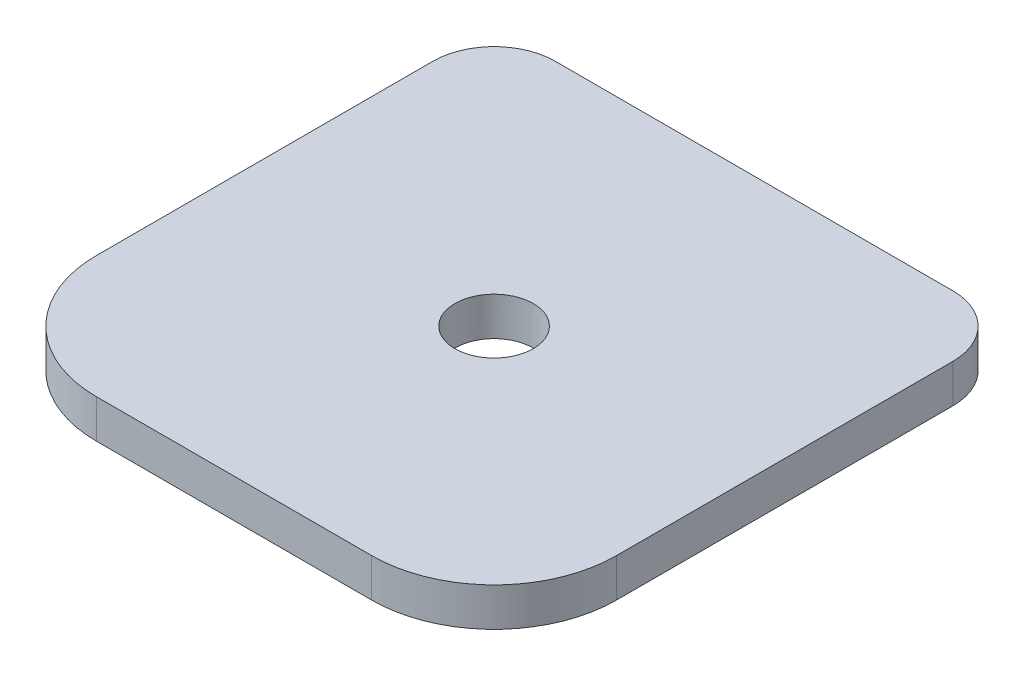
SolidWorks part; units mm, degrees
ref_plane "Front Plane" through (0, 0, 0) normal (0, 0, 1) x (1, 0, 0)
ref_plane "Top Plane" through (0, 0, 0) normal (0, 1, 0) x (1, 0, 0)
ref_plane "Right Plane" through (0, 0, 0) normal (1, 0, 0) x (0, 0, -1)
sketch "Sketch1" plane through (0, 0, 0) normal (0, 1, 0) x (1, 0, 0)
  line L1 (0, 0) -> (85, 0)
  line L2 (0, 0) -> (0, 85)
  line L3 (0, 85) -> (85, 85)
  line L4 (85, 0) -> (85, 85)
  dimension "D1" = 85
  dimension "D2" = 85
extrude "Boss-Extrude1" add sketch "Sketch1" along normal blind 6.3
sketch "Sketch2" plane through (0, 6.3, 0) normal (0, 1, 0) x (1, 0, 0)
  line L0 (0, 85) -> (85, 0) construction
  circle A0 centre (42.5, 42.5) radius 6.4
  dimension "D1" = 12.8
extrude "Cut-Extrude1" cut sketch "Sketch2" against normal up to next
fillet "Fillet1" radius 10 2 edges at (85, 3.15, -85) (0, 3.15, -85)
fillet "Fillet2" radius 20 2 edges at (0, 3.15, 0) (85, 3.15, 0)
